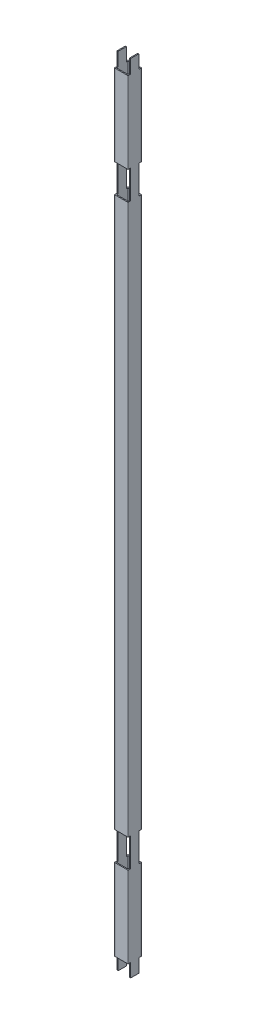
SolidWorks part; units mm, degrees
ref_plane "Front Plane" through (0, 0, 0) normal (0, 0, 1) x (1, 0, 0)
ref_plane "Top Plane" through (0, 0, 0) normal (0, 1, 0) x (1, 0, 0)
ref_plane "Right Plane" through (0, 0, 0) normal (1, 0, 0) x (0, 0, -1)
sketch "Sketch1" plane through (0, 0, 0) normal (0, 1, 0) x (1, 0, 0)
  line L0 (1.5, 1.5) -> (18.5, 1.5)
  line L1 (0.5, 0) -> (19.5, 0)
  line L2 (0, 0.5) -> (0, 19.5)
  line L3 (0.5, 20) -> (19.5, 20)
  line L4 (20, 0.5) -> (20, 19.5)
  line L5 (18.5, 1.5) -> (18.5, 18.5)
  line L6 (1.5, 18.5) -> (18.5, 18.5)
  line L7 (1.5, 1.5) -> (1.5, 18.5)
  arc A0 (19.5, 0) -> (20, 0.5) centre (19.5, 0.5) ccw
  arc A1 (0.5, 0) -> (0, 0.5) centre (0.5, 0.5) cw
  arc A2 (0, 19.5) -> (0.5, 20) centre (0.5, 19.5) cw
  arc A3 (19.5, 20) -> (20, 19.5) centre (19.5, 19.5) cw
  arc A4 (18.5, 1.5) -> (18.5, 1.5) centre (18.5, 1.5) ccw
  arc A5 (18.5, 18.5) -> (18.5, 18.5) centre (18.5, 18.5) cw
  arc A6 (1.5, 18.5) -> (1.5, 18.5) centre (1.5, 18.5) cw
  arc A7 (1.5, 1.5) -> (1.5, 1.5) centre (1.5, 1.5) cw
  point P9 (0, 0)
  dimension "D3" = 0.5
  dimension "D1" = 20
  dimension "D2" = 20
  dimension "D4" = 1.5
extrude "Boss-Extrude1" add sketch "Sketch1" along normal blind 1177
sketch "Sketch3" plane through (0, 0, 0) normal (-1, 0, 0) x (0, 0, 1)
  line L0 (-10, 1177) -> (-10, 957) construction
  line L1 (0, 1177) -> (-4, 1177)
  line L2 (0, 1177) -> (0, 1157)
  line L3 (0, 1157) -> (-4, 1157)
  line L4 (-4, 1177) -> (-4, 1157)
  line L5 (-19.5, 1177) -> (-0.5, 1177) construction
  line L6 (-16, 1177) -> (-16, 1157)
  line L7 (-20, 1157) -> (-16, 1157)
  line L8 (-20, 1177) -> (-20, 1157)
  line L9 (-20, 1177) -> (-16, 1177)
  dimension "D1" = 20
  dimension "D2" = 4
extrude "Cut-Extrude2" cut sketch "Sketch3" against normal blind 977
sketch "Sketch2" plane through (0, 0, 0) normal (-1, 0, 0) x (0, 0, 1)
  line L8 (0, 1157) -> (0, 0) construction
  line L15 (0, 1037) -> (-4, 1037)
  line L16 (0, 1037) -> (0, 994.8)
  line L17 (0, 994.8) -> (-4, 994.8)
  line L18 (-4, 1037) -> (-4, 994.8)
  line L19 (-16, 1177) -> (-4, 1177) construction
  line L20 (-10, 1177) -> (-10, 928.9973) construction
  line L21 (-16, 1037) -> (-16, 994.8)
  line L22 (-20, 994.8) -> (-16, 994.8)
  line L23 (-20, 1037) -> (-20, 994.8)
  line L24 (-20, 1037) -> (-16, 1037)
  dimension "D1" = 42.2
  dimension "D2" = 4
  dimension "D3" = 140
extrude "Cut-Extrude1" cut sketch "Sketch2" against normal through all
ref_plane "Plane1" through (0, 588.5, 0) normal (0, 1, 0) x (1, 0, 0)
mirror "Mirror1" about plane through (0, 588.5, 0) normal (0, 1, 0) of "Cut-Extrude1", "Cut-Extrude2"
